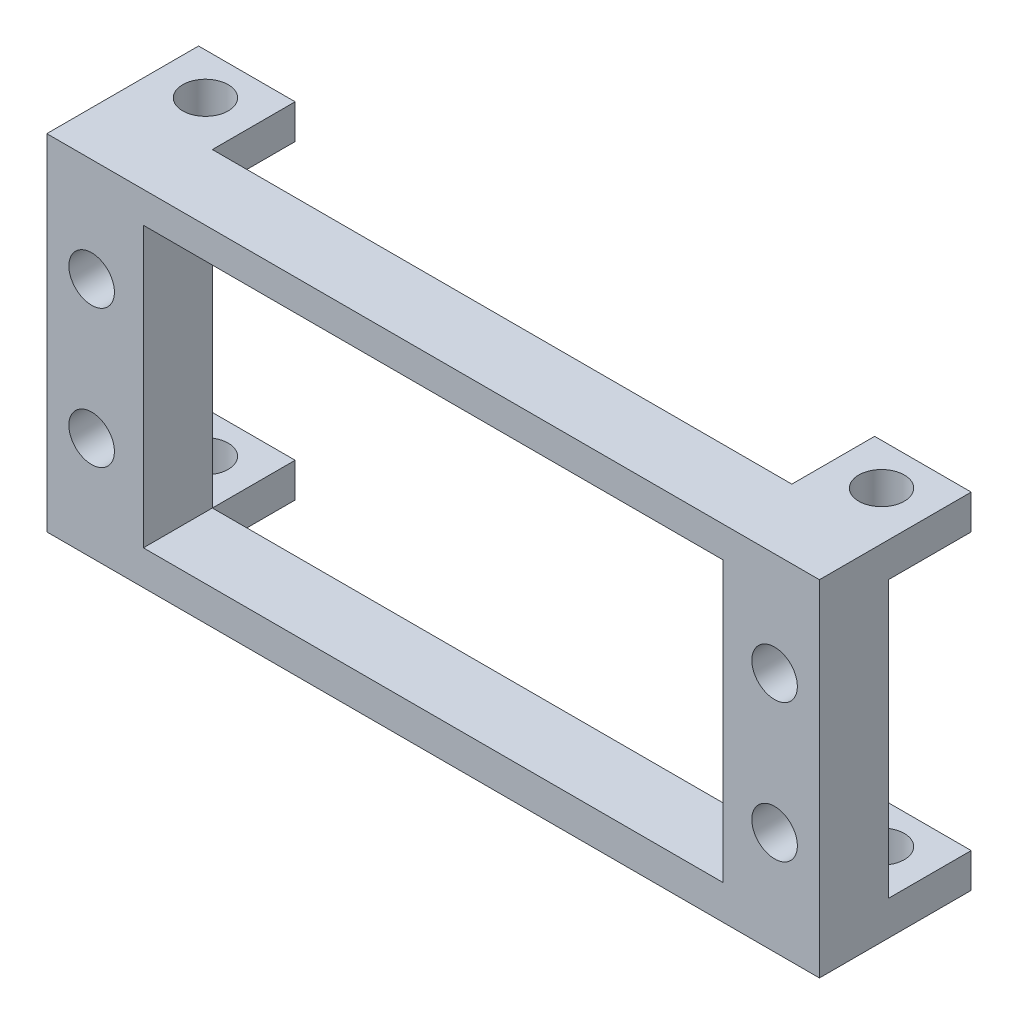
SolidWorks part; units mm, degrees
material "1060 Alloy"
ref_plane "Front Plane" through (0, 0, 0) normal (0, 0, 1) x (1, 0, 0)
ref_plane "Top Plane" through (0, 0, 0) normal (0, 1, 0) x (1, 0, 0)
ref_plane "Right Plane" through (0, 0, 0) normal (1, 0, 0) x (0, 0, -1)
sketch "Sketch1" plane through (0, 0, 0) normal (0, 0, 1) x (1, 0, 0)
  line L0 (-56, 0) -> (0, 0)
  line L1 (0, 0) -> (0, 25)
  line L2 (-49, 2.5) -> (-49, 22.75)
  line L3 (-7, 22.75) -> (-7, 2.5)
  line L4 (-7, 2.5) -> (-49, 2.5)
  line L5 (-56, 0) -> (-56, 25)
  line L6 (-56, 25) -> (0, 25)
  line L7 (-49, 22.75) -> (-7, 22.75)
  dimension "D1" = 2.5
  dimension "D2" = 7
  dimension "D3" = 42
  dimension "D4" = 25
  dimension "D5" = 7
  dimension "D6" = 2.25
extrude "Extrude1" add sketch "Sketch1" along normal blind 5
ref_plane "Plane1" through (0, 0, -22) normal (0, 0, 1) x (1, 0, 0)
hole_wizard "M4x0.7 Tapped Hole1" positions "3DSketch1" profile "Sketch6" tap size "M4x0.7" standard "Ansi Metric" end condition through all
sketch3d "3DSketch1"
  line L1 (-56, 0, 5) -> (0, 0, 5) construction
  line L2 (0, 25, 5) -> (-56, 25, 5) construction
  line L7 (-49, 22.75, 5) -> (-49, 2.5, 5) construction
  line L8 (-7, 2.5, 5) -> (-7, 22.75, 5) construction
  point P0 (-52.75, 17.5, 5)
  point P2 (-52.75, 7.5, 5)
  point P4 (-3.25, 7.5, 5)
  point P6 (-3.25, 17.5, 5)
  dimension "D1" = 49.5
  dimension "D2" = 49.5
  dimension "D6" = 3.75
  dimension "D3" = 10
  dimension "D4" = 7.5
  dimension "D5" = 7.5
  dimension "D8" = 3.75
  dimension "D7" = 10
sketch "Sketch6" plane through (-52.75, 17.5, 5) normal (1, 0, 0) x (0, -1, 0)
  line L0 (0, 0) -> (0, 5)
  line L1 (0, 5) -> (1.65, 5)
  line L2 (1.65, 5) -> (1.65, 0)
  line L5 (1.65, 0) -> (0, 0)
  line L11 (0, -6.35) -> (0, 107.95) construction
  dimension "Thru Tap Drill Dia." = 3.3
  dimension "Thru Tap Drill Depth" = 5
cosmetic thread "Hole Thread1" parameters "D2"=4
cosmetic thread "Hole Thread2" parameters "D2"=4
cosmetic thread "Hole Thread3" parameters "D2"=4
cosmetic thread "Hole Thread4" parameters "D2"=4
sketch "Sketch7" plane through (0, 0, 0) normal (0, 0, -1) x (-1, 0, 0)
  line L0 (7, 2.5) -> (7, 22.75) construction
  line L1 (0, 25) -> (7, 25)
  line L2 (0, 25) -> (0, 22.5)
  line L3 (0, 22.5) -> (7, 22.5)
  line L4 (7, 25) -> (7, 22.5)
  line L5 (49, 22.75) -> (49, 2.5) construction
  line L6 (0, 0) -> (7, 0)
  line L7 (0, 0) -> (0, 2.5)
  line L8 (0, 2.5) -> (7, 2.5)
  line L9 (7, 0) -> (7, 2.5)
  line L10 (56, 0) -> (49, 0)
  line L11 (56, 0) -> (56, 2.5)
  line L12 (56, 2.5) -> (49, 2.5)
  line L13 (49, 0) -> (49, 2.5)
  line L15 (56, 25) -> (49, 25)
  line L16 (56, 25) -> (56, 22.5)
  line L17 (56, 22.5) -> (49, 22.5)
  line L18 (49, 25) -> (49, 22.5)
  dimension "D1" = 2.5
  dimension "D2" = 2.5
  dimension "D3" = 2.5
  dimension "D4" = 2.5
extrude "Extrude5" add sketch "Sketch7" along normal blind 6
hole_wizard "M4x0.7 Tapped Hole2" positions "3DSketch2" profile "Sketch8" tap size "M4x0.7" standard "Ansi Metric"
sketch3d "3DSketch2"
  line L2 (-7, 25, -6) -> (0, 25, -6) construction
  line L3 (0, 25, 5) -> (0, 25, -6) construction
  line L4 (-56, 25, 5) -> (-56, 25, -6) construction
  line L5 (-56, 25, -6) -> (-49, 25, -6) construction
  point P0 (-3.5, 25, -3)
  point P4 (-52.5, 25, -3)
  point P6 (-3.5, 0, -3)
  point P10 (-52.5, 0, -3)
  dimension "D3" = 3
  dimension "D4" = 3.5
  dimension "D5" = 3.5
  dimension "D6" = 3
sketch "Sketch8" plane through (-3.5, 25, -3) normal (1, 0, 0) x (0, 0, 1)
  line L0 (0, 0) -> (0, 11.2914)
  line L1 (0, 11.2914) -> (1.65, 10.3)
  line L2 (1.65, 10.3) -> (1.65, 0)
  line L5 (1.65, 0) -> (0, 0)
  line L10 (0, 11.2914) -> (-1.65, 10.3) construction
  line L11 (0, -6.35) -> (0, 107.95) construction
  dimension "Tap Drill Dia." = 3.3
  dimension "Tap Drill Depth" = 10.3
  dimension "Drill Angle" = 118
cosmetic thread "Hole Thread5"
cosmetic thread "Hole Thread6"
cosmetic thread "Hole Thread7"
cosmetic thread "Hole Thread8"
